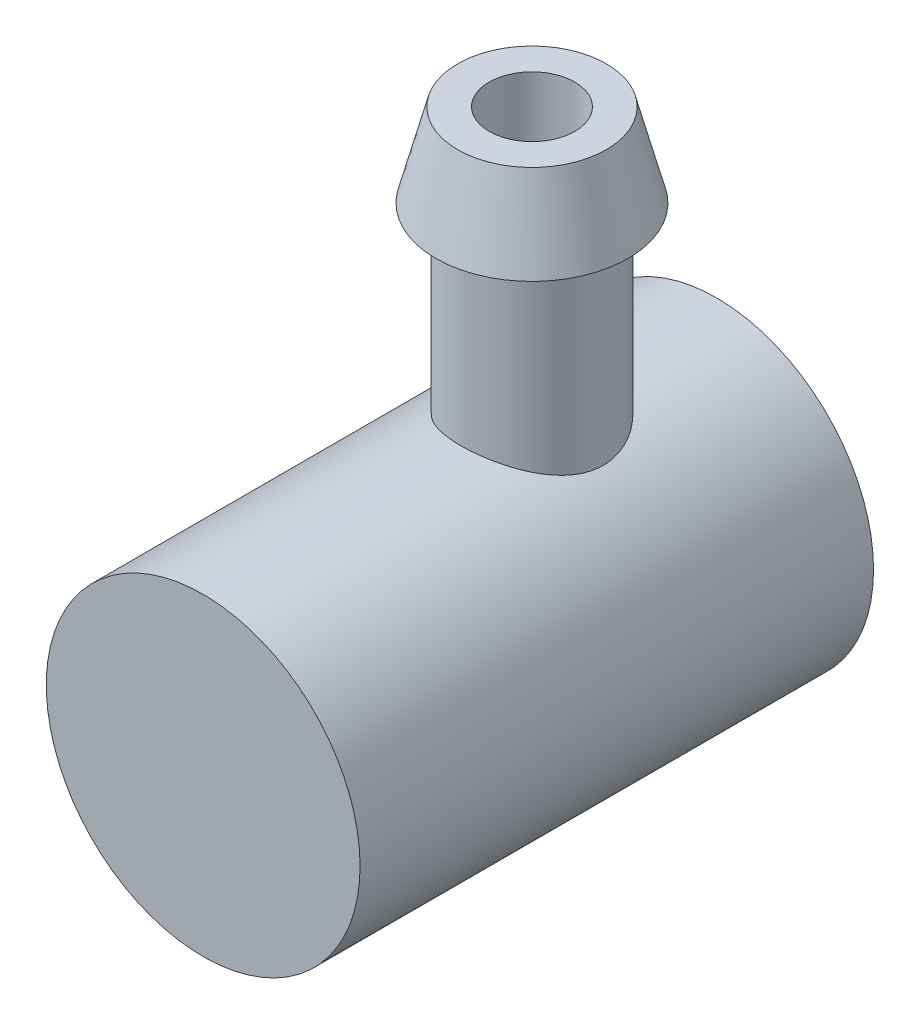
SolidWorks part; units mm, degrees
ref_plane "Front Plane" through (0, 0, 0) normal (0, 0, 1) x (1, 0, 0)
ref_plane "Top Plane" through (0, 0, 0) normal (0, 1, 0) x (1, 0, 0)
ref_plane "Right Plane" through (0, 0, 0) normal (1, 0, 0) x (0, 0, -1)
sketch "Sketch1" plane through (0, 0, 0) normal (0, 0, 1) x (1, 0, 0)
  circle A0 centre (0, 0) radius 5.5
  dimension "D1" = 11
extrude "Boss-Extrude1" add sketch "Sketch1" against normal blind 18
sketch "Sketch3" plane through (0, 0, 0) normal (1, 0, 0) x (0, 0, -1)
  line L1 (13.0263, 14.5396) -> (14.1339, 14.5396)
  line L2 (14.1339, 14.5396) -> (14.8978, 11.6191)
  line L3 (14.8978, 11.6191) -> (14.0263, 11.6191)
  line L4 (14.0263, 11.6191) -> (14.0263, 0.0396)
  line L5 (14.0263, 0.0396) -> (13.0263, 0.0396)
  line L6 (13.0263, 14.5396) -> (13.0263, 0.0396)
  line L7 (11.5263, 14.5396) -> (11.5263, 0.0396) construction
  point P8 (0, 0)
  point P9 (0, 0)
  point P10 (0, 0)
  point P11 (0, 0)
  point P12 (0, 0)
  point P13 (0, 0)
  point P14 (0, 0)
  point P15 (15.3978, 11.6191)
  dimension "D1" = 14.5
  dimension "D2" = 2.5
  dimension "D3" = 1.5
revolve "Revolve1" add sketch "Sketch3" angle 360 about L7
